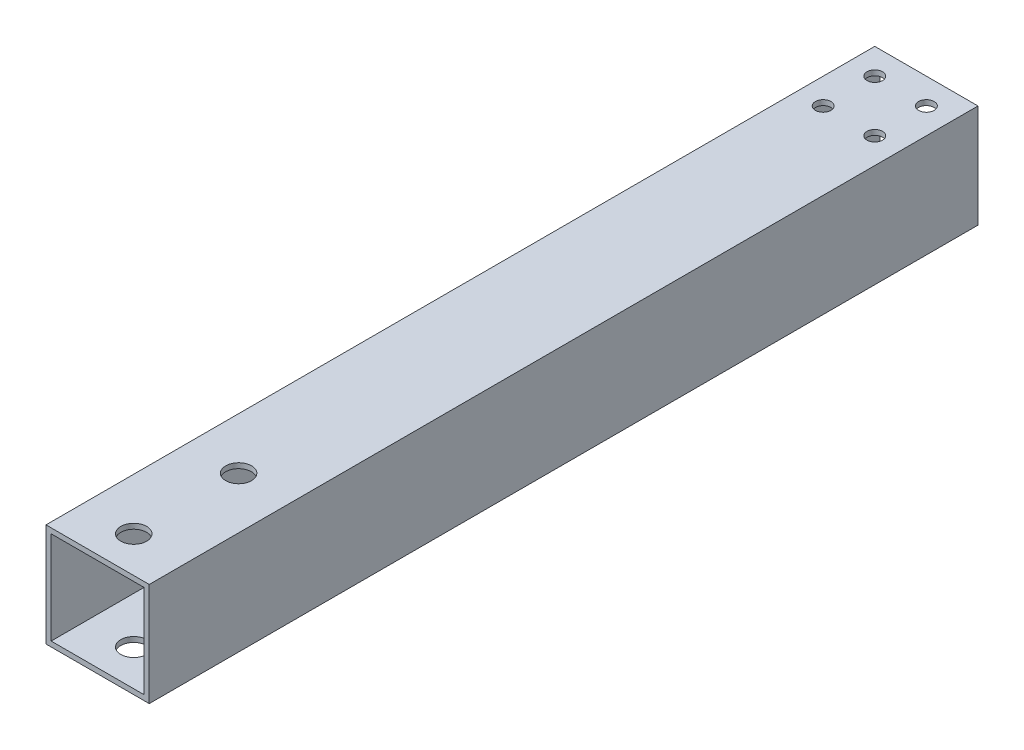
SolidWorks part; units mm, degrees
ref_plane "前视基准面" through (0, 0, 0) normal (0, 0, 1) x (1, 0, 0)
ref_plane "上视基准面" through (0, 0, 0) normal (0, 1, 0) x (1, 0, 0)
ref_plane "右视基准面" through (0, 0, 0) normal (1, 0, 0) x (0, 0, -1)
sketch "草图1" plane through (0, 0, 0) normal (0, 0, 1) x (1, 0, 0)
  line L1 (-10, 10) -> (10, 10)
  line L2 (-10, 10) -> (-10, -10)
  line L3 (-10, -10) -> (10, -10)
  line L4 (10, 10) -> (10, -10)
  line L5 (-10, 10) -> (10, -10) construction
  line L6 (-10, -10) -> (10, 10) construction
  line L7 (-9, 9) -> (9, 9)
  line L8 (-9, 9) -> (-9, -9)
  line L9 (-9, -9) -> (9, -9)
  line L10 (9, 9) -> (9, -9)
  line L11 (-9, 9) -> (9, -9) construction
  line L12 (-9, -9) -> (9, 9) construction
  point P0 (0, 0)
  point P6 (0, 0)
  dimension "D1" = 20
  dimension "D2" = 20
  dimension "D3" = 18
  dimension "D4" = 18
extrude "凸台-拉伸1" add sketch "草图1" along normal blind 171.98
sketch "草图2" plane through (0, 10, 0) normal (0, 1, 0) x (1, 0, 0)
  line L0 (10, 0) -> (-10, 0) construction
  line L1 (-10, -171.98) -> (-10, 0) construction
  circle A0 centre (-5, -5) radius 1.5
  circle A1 centre (5, -5) radius 1.5
  circle A2 centre (-5, -15) radius 1.5
  circle A3 centre (5, -15) radius 1.5
  circle A4 centre (-5, -235) radius 1.5
  circle A5 centre (5, -245) radius 1.5
  circle A6 centre (5, -235) radius 1.5
  circle A7 centre (-5, -245) radius 1.5
  dimension "D4" = 3
  dimension "D5" = 3
  dimension "D6" = 3
  dimension "D7" = 3
  dimension "D1" = 10
  dimension "D2" = 10
  dimension "D3" = 10
  dimension "D8" = 5
  dimension "D9" = 5
extrude "切除-拉伸1" cut sketch "草图2" against normal blind 50
sketch "草图4" plane through (0, -10, 0) normal (0, -1, 0) x (1, 0, 0)
  line L0 (10, 171.98) -> (10, 163.58)
  line L1 (10, 171.98) -> (10, 0) construction
  line L2 (10, 163.58) -> (-10, 163.58)
  line L3 (-10, 171.98) -> (-10, 0) construction
  line L4 (-10, 163.58) -> (-10, 171.98)
  line L5 (-10, 171.98) -> (10, 171.98)
extrude "切除-拉伸2" cut sketch "草图4" against normal through all
sketch "草图5" plane through (0, 10, 0) normal (0, 1, 0) x (1, 0, 0)
  circle A0 centre (0, -153.58) radius 2.5
  circle A1 centre (0, -133.26) radius 2.5
extrude "切除-拉伸3" cut sketch "草图5" against normal blind 36
sketch "草图6" plane through (0, 10, 0) normal (0, 1, 0) x (1, 0, 0)
  line L0 (-10, -163.58) -> (-10, -160.58)
  line L1 (-10, -163.58) -> (-10, 0) construction
  line L2 (-10, -160.58) -> (10, -160.58)
  line L3 (10, -163.58) -> (10, 0) construction
  line L4 (10, -160.58) -> (10, -163.58)
  line L5 (10, -163.58) -> (-10, -163.58)
extrude "切除-拉伸4" cut sketch "草图6" against normal blind 33 contours L2 L4 L5 L0
